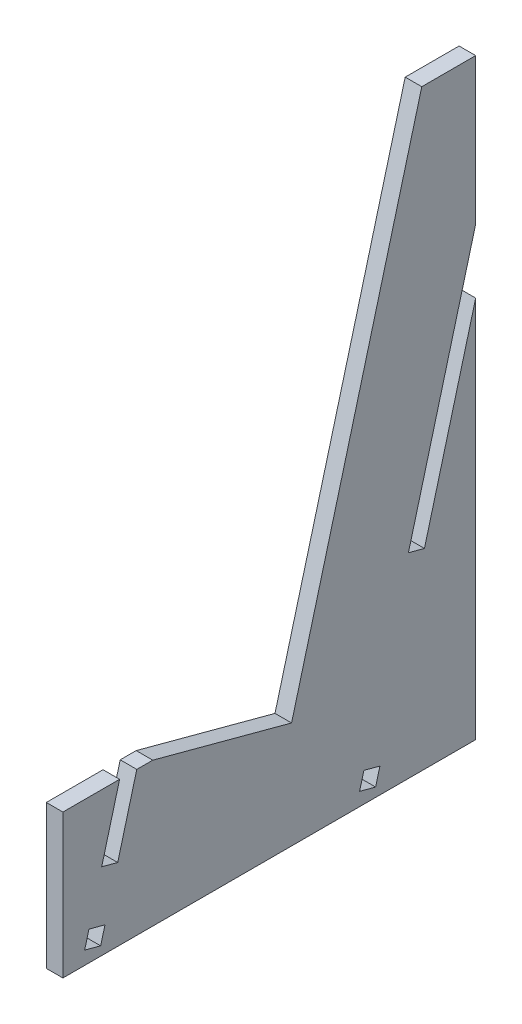
SolidWorks part; units mm, degrees
ref_plane "Front Plane" through (0, 0, 0) normal (0, 0, 1) x (1, 0, 0)
ref_plane "Top Plane" through (0, 0, 0) normal (0, 1, 0) x (1, 0, 0)
ref_plane "Right Plane" through (0, 0, 0) normal (1, 0, 0) x (0, 0, -1)
sketch "Sketch1" plane through (0, 0, 0) normal (1, 0, 0) x (0, 0, -1)
  line L6 (0, 0) -> (0, 104.6968)
  line L7 (0, 104.6968) -> (-9.525, 104.6968)
  line L8 (-9.525, 104.6968) -> (-32.534, 18.826)
  line L9 (-32.534, 18.826) -> (-57.0685, 25.4)
  line L10 (-57.0685, 25.4) -> (-72.9435, 25.4)
  line L11 (-72.9435, 25.4) -> (-72.9435, 0)
  line L12 (-72.9435, 0) -> (0, 0)
  dimension "D1" = 25.4
  dimension "D2" = 15
  dimension "D3" = 88.9
  dimension "D4" = 25.4
  dimension "D5" = 9.525
  dimension "D6" = 15.875
extrude "Boss-Extrude1" add sketch "Sketch1" along normal blind 2.93
sketch "Sketch2" plane through (2.93, 0, 0) normal (1, 0, 0) x (0, 0, -1)
  line L0 (-57.0685, 25.4) -> (-72.9435, 25.4) construction
  line L1 (-69.7685, 25.4) -> (-66.8385, 25.4)
  line L2 (-69.7685, 25.4) -> (-69.7685, 12.7)
  line L3 (-69.7685, 12.7) -> (-66.8385, 12.7)
  line L4 (-66.8385, 25.4) -> (-66.8385, 12.7)
  line L5 (-72.9435, 25.4) -> (-72.9435, 0) construction
  line L6 (-72.9435, 25.4) -> (-72.9435, 0)
  point P8 (-72.9435, 12.7)
  line M11 (-57.0685, 25.4) -> (-72.9435, 25.4)
  dimension "D1" = 2.93
  dimension "D2" = 3.175
extrude "Cut-Extrude1" [suppressed] cut sketch "Sketch2" against normal through all contours L4 L2 L3 M11
sketch "Sketch3" plane through (2.93, 0, 0) normal (1, 0, 0) x (0, 0, -1)
  line L1 (0, 0) -> (-2.93, 0)
  line L2 (0, 0) -> (0, 10)
  line L3 (0, 10) -> (-2.93, 10)
  line L4 (-2.93, 0) -> (-2.93, 10)
  dimension "D1" = 2.93
  dimension "D2" = 10
extrude "Cut-Extrude2" [suppressed] cut sketch "Sketch3" against normal through all
pattern_linear "LPattern1" [suppressed] count 7 spacing 20
sketch "Sketch4" plane through (2.93, 0, 0) normal (1, 0, 0) x (0, 0, -1)
  line L0 (0, 0) -> (0, 104.6968) construction
  line L1 (0, 10) -> (-2.93, 10)
  line L2 (0, 10) -> (0, 20)
  line L3 (0, 20) -> (-2.93, 20)
  line L4 (-2.93, 10) -> (-2.93, 20)
  line L5 (-72.9435, 0) -> (0, 0) construction
  dimension "D1" = 10
  dimension "D2" = 2.93
  dimension "D3" = 10
extrude "Cut-Extrude3" [suppressed] cut sketch "Sketch4" against normal through all
pattern_linear "LPattern2" [suppressed] count 7 spacing 20
sketch "Sketch5" plane through (2.93, 0, 0) normal (1, 0, 0) x (0, 0, -1)
  line L0 (0, 78.9083) -> (-11.8852, 34.5522)
  line L1 (0, 78.9083) -> (2.8302, 78.15)
  line L2 (-11.8852, 34.5522) -> (-9.055, 33.7938)
  line L3 (2.8302, 78.15) -> (-9.055, 33.7938)
  line L4 (0, 78.9083) -> (-9.055, 33.7938) construction
  line L5 (-11.8852, 34.5522) -> (2.8302, 78.15) construction
  line L6 (-9.525, 104.6968) -> (-32.534, 18.826) construction
  line L7 (0, 0) -> (0, 104.6968) construction
  line L8 (0, 0) -> (0, 67.5876)
  point P1 (-4.5275, 56.3511)
  point P3 (0, 33.7938)
  line M7 (0, 0) -> (0, 104.6968)
  dimension "D1" = 2.93
  dimension "D2" = 15.875
extrude "Cut-Extrude4" cut sketch "Sketch5" against normal through all contours L3 L0 L2 M7
sketch "Sketch6" plane through (0, 0, 0) normal (-1, 0, 0) x (0, 0, 1)
  line L1 (72.9435, 0) -> (70.0135, 0)
  line L2 (72.9435, 0) -> (72.9435, 10)
  line L3 (72.9435, 10) -> (70.0135, 10)
  line L4 (70.0135, 0) -> (70.0135, 10)
  dimension "D1" = 10
  dimension "D2" = 2.93
extrude "Cut-Extrude5" [suppressed] cut sketch "Sketch6" against normal through all
pattern_linear "LPattern3" [suppressed] count 2 spacing 20
sketch "Sketch7" plane through (0, 0, 0) normal (-1, 0, 0) x (0, 0, 1)
  line L0 (60.2435, 24.0775) -> (66.2697, 1.5875) construction
  line L1 (60.2435, 24.0775) -> (63.0737, 24.8358) construction
  line L2 (66.2697, 1.5875) -> (69.0999, 2.3458) construction
  line L3 (63.0737, 24.8358) -> (69.0999, 2.3458) construction
  line L4 (60.2435, 24.0775) -> (69.0999, 2.3458) construction
  line L5 (66.2697, 1.5875) -> (63.0737, 24.8358) construction
  line L6 (9.525, 104.6968) -> (32.534, 18.826) construction
  line L7 (63.2566, 12.8325) -> (66.0868, 13.5908)
  line L8 (72.9435, 0) -> (0, 0) construction
  line L9 (63.2566, 12.8325) -> (59.8892, 25.4)
  line L10 (66.0868, 13.5908) -> (62.7193, 26.1583)
  line L11 (59.8892, 25.4) -> (62.7193, 26.1583)
  line L12 (57.0685, 25.4) -> (72.9435, 25.4) construction
  point P1 (64.6717, 13.2117)
  dimension "D2" = 2.93
  dimension "D1" = 3.175
  dimension "D3" = 23.2833
  dimension "D4" = 1.5875
extrude "Cut-Extrude6" cut sketch "Sketch7" against normal through all
sketch "Sketch9" plane through (0, 0, 0) normal (-1, 0, 0) x (0, 0, 1)
  line L0 (66.2697, 1.5875) -> (69.0999, 2.3458) construction
  line L1 (66.2697, 1.5875) -> (69.0999, 2.3458)
  line L2 (66.2697, 1.5875) -> (69.0999, 2.3458)
  line L3 (66.2697, 1.5875) -> (65.5114, 4.4177)
  line L4 (69.0999, 2.3458) -> (68.3415, 5.176)
  line L5 (65.5114, 4.4177) -> (68.3415, 5.176)
extrude "Cut-Extrude7" cut sketch "Sketch9" against normal through all contours L5 L3 L1 L4
fillet "Fillet1" [suppressed] radius 0.5
fillet "Fillet2" [suppressed] radius 1
sketch "Sketch11" plane through (0, 0, 0) normal (-1, 0, 0) x (0, 0, 1)
  line L0 (17.6834, 1.5923) -> (20.5136, 2.3506)
  line L1 (17.6834, 1.5923) -> (16.9251, 4.4224)
  line L2 (20.5136, 2.3506) -> (19.7552, 5.1808)
  line L3 (16.9251, 4.4224) -> (19.7552, 5.1808)
  line L4 (11.8852, 34.5522) -> (9.055, 33.7938) construction
  line L6 (0, 67.5876) -> (9.055, 33.7938) construction
  line L7 (0, 78.9083) -> (11.8852, 34.5522) construction
  dimension "D2" = 2.93
  dimension "D1" = 33.3375
extrude "Cut-Extrude9" cut sketch "Sketch11" against normal through all
equation "\"thick\"= 2.93mm'Acrylic thickness"
equation "\"D1@Boss-Extrude1\"=\"thick\""
equation "\"D1@Sketch2\"=\"thick\""
equation "\"slot\"= 10mm'Slot width"
equation "\"D1@Sketch3\"=\"thick\""
equation "\"D2@Sketch3\"=\"slot\""
equation "\"D3@LPattern1\"=2*\"slot\""
equation "\"D1@Sketch4\"=\"slot\""
equation "\"D2@Sketch4\"=\"thick\""
equation "\"D3@Sketch4\"=\"slot\""
equation "\"D3@LPattern2\"=2*\"slot\""
equation "\"D1@Sketch5\"=\"thick\""
equation "\"D1@Sketch6\"=\"slot\""
equation "\"D2@Sketch6\"=\"thick\""
equation "\"D3@LPattern3\"=2 * \"slot\""
equation "\"D2@Sketch7\"=\"thick\""
equation "\"D2@Sketch11\"=\"thick\""
